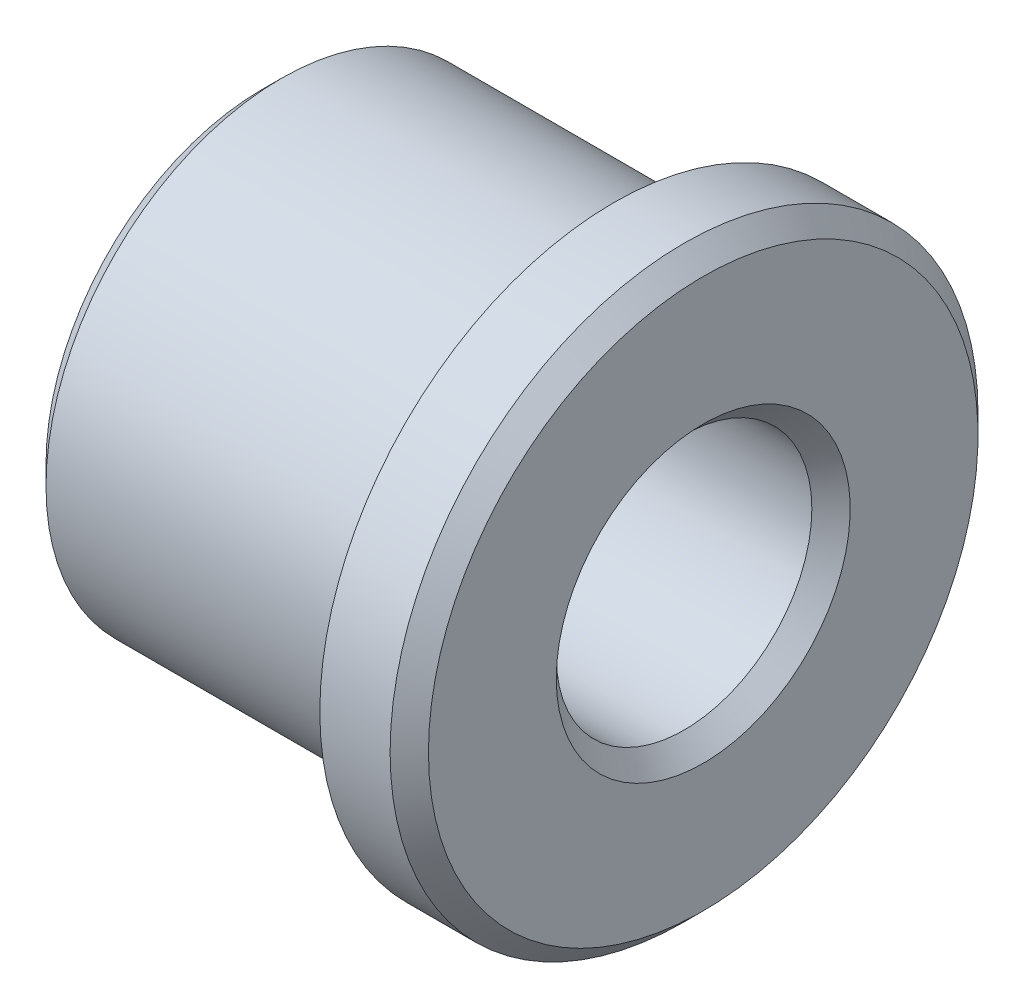
SolidWorks part; units mm, degrees
material "PA Type 6"
ref_plane "Plan de face" through (0, 0, 0) normal (0, 0, 1) x (1, 0, 0)
ref_plane "Plan de dessus" through (0, 0, 0) normal (0, 1, 0) x (1, 0, 0)
ref_plane "Plan de droite" through (0, 0, 0) normal (1, 0, 0) x (0, 0, -1)
sketch "Esquisse1" plane through (0, 0, 0) normal (0, 0, 1) x (1, 0, 0)
  line L0 (0, 10) -> (0, 18.425)
  line L1 (0, 18.425) -> (27.5, 18.425)
  line L2 (-4.4443, 0) -> (40.5682, 0) construction
  line L3 (34.5, 10) -> (34.5, 23)
  line L4 (34.5, 23) -> (27.5, 23)
  line L5 (27.5, 23) -> (27.5, 18.425)
  line L7 (0, 10) -> (34.5, 10)
  dimension "D1" = 7
  dimension "D2" = 34.5
revolve "Révolution1" add sketch "Esquisse1" angle 360 about L2
chamfer "Chanfrein1" distance 1.5 angle 45 4 edges at (34.5, 0, 10) (34.5, 0, 23) (0, 0, 18.425) (0, 0, 10)
